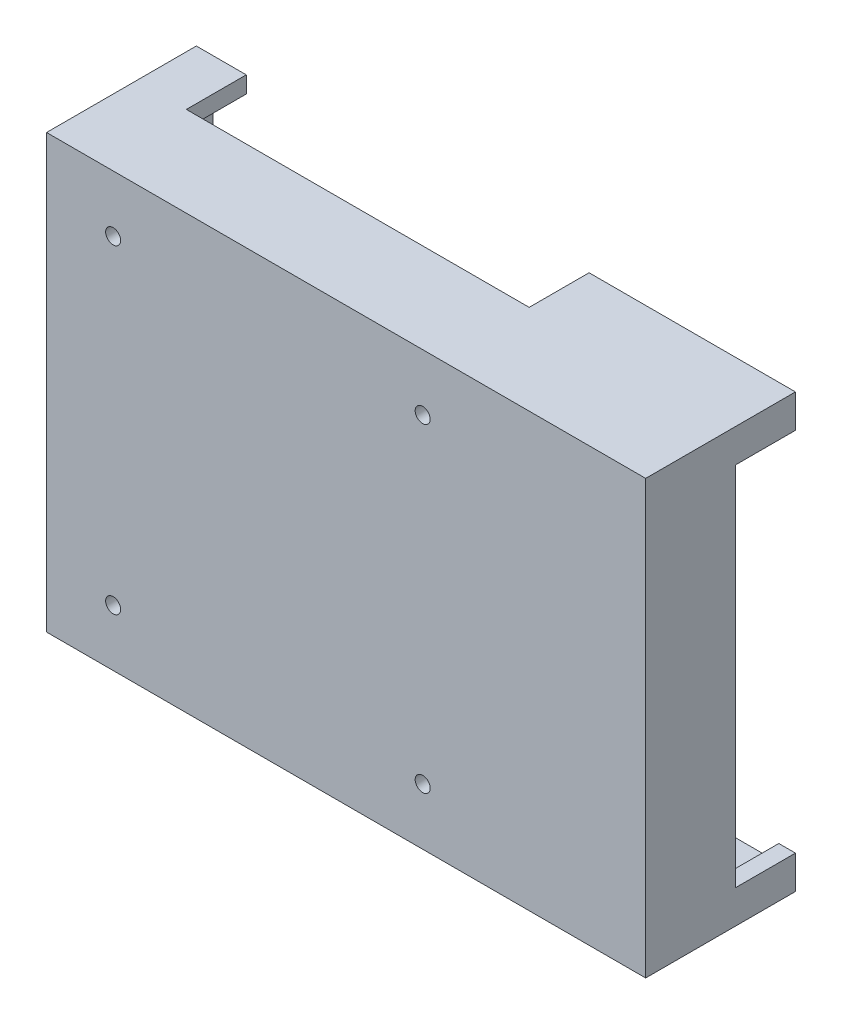
SolidWorks part; units mm, degrees
ref_plane "Front Plane" through (0, 0, 0) normal (0, 0, 1) x (1, 0, 0)
ref_plane "Top Plane" through (0, 0, 0) normal (0, 1, 0) x (1, 0, 0)
ref_plane "Right Plane" through (0, 0, 0) normal (1, 0, 0) x (0, 0, -1)
sketch "Sketch1" plane through (0, 0, 0) normal (0, 0, 1) x (1, 0, 0)
  line L1 (90, -65) -> (-90, -65)
  line L2 (90, -65) -> (90, 65)
  line L3 (90, 65) -> (-90, 65)
  line L4 (-90, -65) -> (-90, 65)
  line L5 (90, -65) -> (-90, 65) construction
  line L6 (90, 65) -> (-90, -65) construction
  point P0 (0, 0)
  point P6 (23, 48)
  point P7 (-70, 48)
  point P8 (-70, -48)
  point P9 (23, -48)
  dimension "D1" = 130
  dimension "D2" = 180
  dimension "D3" = 96
  dimension "D4" = 93
  dimension "D5" = 20
  dimension "D6" = 17
extrude "Boss-Extrude1" add sketch "Sketch1" along normal blind 45
sketch "Sketch3" plane through (0, 0, 0) normal (0, 0, 1) x (1, 0, 0)
  line L0 (90, -65) -> (90, 65) construction
  line L1 (-85, -60) -> (85, -60)
  line L2 (-85, -60) -> (-85, 60)
  line L3 (-85, 60) -> (85, 60)
  line L4 (85, -60) -> (85, 60)
  line L5 (-85, -60) -> (85, 60) construction
  line L6 (-85, 60) -> (85, -60) construction
  line L8 (90, 65) -> (-90, 65) construction
  point P0 (0, 0)
  dimension "D1" = 5
  dimension "D2" = 5
extrude "Cut-Extrude1" cut sketch "Sketch3" along normal blind 40
hole_wizard "M4 Clearance Hole1" positions "Sketch4" profile "Sketch5" hole size "M4" standard "ANSI Metric" end condition through all
sketch "Sketch4" plane through (0, 0, 40) normal (0, 0, -1) x (-1, 0, 0)
  point P0 (-23, -48)
  point P3 (70, -48)
  point P6 (70, 48)
  point P9 (-23, 48)
sketch "Sketch5" plane through (23, -48, 40) normal (1, 0, 0) x (0, 1, 0)
  line L0 (0, 0) -> (0, 5)
  line L1 (0, 5) -> (2.25, 5)
  line L2 (2.25, 5) -> (2.25, 0)
  line L5 (2.25, 0) -> (0, 0)
  line L11 (0, -6.35) -> (0, 107.95) construction
  dimension "Thru Hole Dia." = 4.5
  dimension "Thru Hole Depth" = 5
sketch "Sketch7" plane through (90, 0, 0) normal (1, 0, 0) x (0, 0, -1)
  line L0 (0, -65) -> (0, 65) construction
  line L1 (0, 55) -> (-18, 55)
  line L2 (0, 55) -> (0, -55)
  line L3 (0, -55) -> (-18, -55)
  line L4 (-18, 55) -> (-18, -55)
  point P6 (0, 0)
  dimension "D1" = 18
  dimension "D2" = 110
extrude "Cut-Extrude2" cut sketch "Sketch7" against normal up to next
sketch "Sketch8" plane through (0, -65, 0) normal (0, -1, 0) x (1, 0, 0)
  line L0 (-90, 0) -> (90, 0) construction
  line L1 (-75, 0) -> (28, 0)
  line L2 (-75, 0) -> (-75, 18)
  line L3 (-75, 18) -> (28, 18)
  line L4 (28, 0) -> (28, 18)
  line L5 (-90, 45) -> (-90, 0) construction
  dimension "D1" = 18
  dimension "D2" = 103
  dimension "D3" = 15
extrude "Cut-Extrude3" cut sketch "Sketch8" against normal up to surface (130 mm away) up to face at (0, 65, 22.5)
